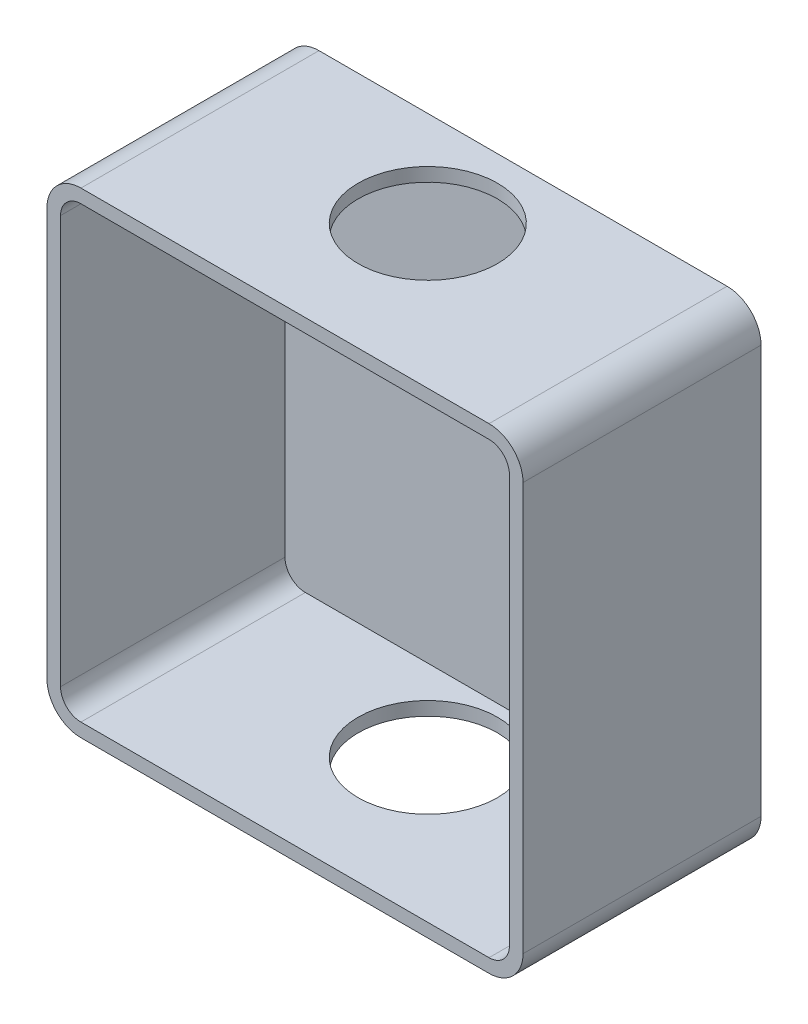
SolidWorks part; units mm, degrees
material "ABS"
ref_plane "Ebene vorne" through (0, 0, 0) normal (0, 0, 1) x (1, 0, 0)
ref_plane "Ebene oben" through (0, 0, 0) normal (0, 1, 0) x (1, 0, 0)
ref_plane "Ebene rechts" through (0, 0, 0) normal (1, 0, 0) x (0, 0, -1)
sketch "Skizze1" plane through (0, 0, 0) normal (0, 0, 1) x (1, 0, 0)
  line L1 (-30, -35) -> (30, -35)
  line L2 (-35, -30) -> (-35, 30)
  line L3 (-30, 35) -> (30, 35)
  line L4 (35, -30) -> (35, 30)
  line L5 (-35, -35) -> (35, 35) construction
  line L6 (-35, 35) -> (35, -35) construction
  arc A0 (-30, -35) -> (-35, -30) centre (-30, -30) cw
  arc A1 (30, -35) -> (35, -30) centre (30, -30) ccw
  arc A2 (30, 35) -> (35, 30) centre (30, 30) cw
  arc A3 (-35, 30) -> (-30, 35) centre (-30, 30) cw
  point P0 (0, 0)
  dimension "D3" = 5
  dimension "D1" = 70
  dimension "D2" = 70
extrude "Aufsatz-Linear austragen1" add sketch "Skizze1" along normal blind 35
shell "Wandung1" thickness 2
sketch "Skizze2" plane through (0, -35, 0) normal (0, -1, 0) x (1, 0, 0)
  circle A0 centre (0, 14) radius 10.25
  dimension "D1" = 20.5
  dimension "D2" = 14
extrude "Schnitt-Linear austragen1" cut sketch "Skizze2" against normal through all
